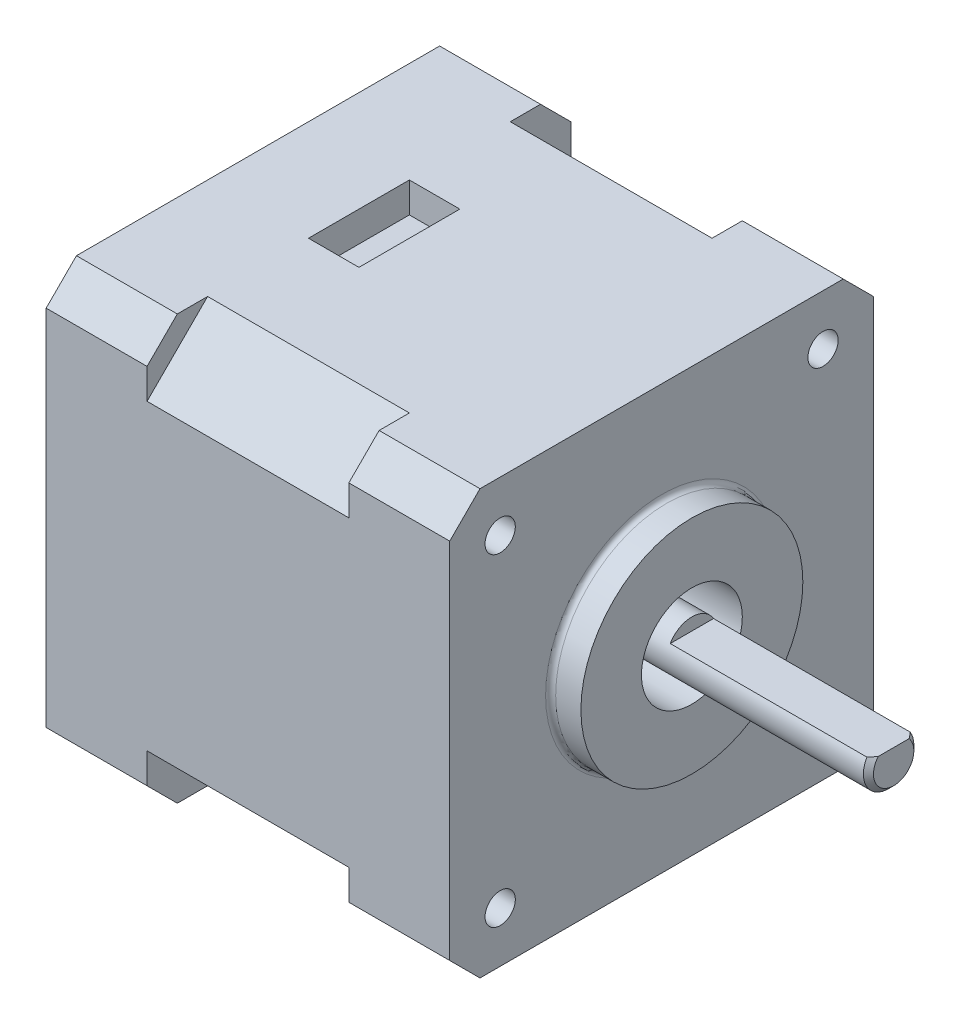
SolidWorks part; units mm, degrees
ref_plane "Plan de face" through (0, 0, 0) normal (0, 0, 1) x (1, 0, 0)
ref_plane "Plan de dessus" through (0, 0, 0) normal (0, 1, 0) x (1, 0, 0)
ref_plane "Plan de droite" through (0, 0, 0) normal (1, 0, 0) x (0, 0, -1)
sketch "Esquisse1" plane through (0, 0, 0) normal (1, 0, 0) x (0, 0, -1)
  line L0 (21, 0) -> (21, -36) construction
  line L1 (6, 0) -> (36, 0)
  line L2 (0, -6) -> (0, -36)
  line L3 (6, -42) -> (36, -42)
  line L4 (42, -6) -> (42, -36)
  line L5 (0, -21) -> (42, -21) construction
  line L6 (6, 0) -> (0, -6)
  line L7 (36, 0) -> (42, -6)
  line L8 (36, -42) -> (42, -36)
  line L9 (6, -42) -> (0, -36)
  dimension "D2" = 15
  dimension "D3" = 15
extrude "Boss.-Extru.1" add sketch "Esquisse1" along normal mid plane 20
sketch "Esquisse2" plane through (10, 0, 0) normal (1, 0, 0) x (0, 0, -1)
  line L0 (21, 0) -> (21, -42) construction
  line L1 (36, 0) -> (6, 0) construction
  line L2 (6, -42) -> (36, -42) construction
  line L3 (0, -21) -> (42, -21) construction
  line L4 (0, -6) -> (0, -36) construction
  line L5 (42, -36) -> (42, -6) construction
  line L7 (0, 0) -> (42, 0)
  line L8 (0, 0) -> (0, -42)
  line L9 (0, -42) -> (42, -42)
  line L10 (42, 0) -> (42, -42)
  line L11 (0, 0) -> (42, -42) construction
  line L12 (0, -42) -> (42, 0) construction
  point P12 (21, -21)
extrude "Boss.-Extru.2" add sketch "Esquisse2" along normal blind 10
sketch "Esquisse3" plane through (-10, 0, 0) normal (-1, 0, 0) x (0, 0, 1)
  line L0 (-21, 0) -> (-21, -42) construction
  line L1 (-36, 0) -> (-6, 0) construction
  line L2 (-6, -42) -> (-36, -42) construction
  line L3 (-42, -21) -> (0, -21) construction
  line L4 (-42, -36) -> (-42, -6) construction
  line L5 (0, -6) -> (0, -36) construction
  line L7 (-42, 0) -> (0, 0)
  line L8 (-42, 0) -> (-42, -42)
  line L9 (-42, -42) -> (0, -42)
  line L10 (0, 0) -> (0, -42)
  line L11 (-42, 0) -> (0, -42) construction
  line L12 (-42, -42) -> (0, 0) construction
  point P12 (-21, -21)
extrude "Boss.-Extru.3" add sketch "Esquisse3" along normal blind 10
sketch "Esquisse4" plane through (20, 0, 0) normal (1, 0, 0) x (0, 0, -1)
  line L0 (21, 0) -> (21, -42) construction
  line L1 (42, 0) -> (0, 0) construction
  line L2 (0, -42) -> (42, -42) construction
  line L3 (0, -21) -> (42, -21) construction
  line L4 (0, 0) -> (0, -42) construction
  line L5 (42, -42) -> (42, 0) construction
  circle A0 centre (21, -21) radius 11
  dimension "D1" = 22
extrude "Boss.-Extru.4" add sketch "Esquisse4" along normal blind 3
fillet "Congé1" radius 0.5 1 edges at (20, -21, -32)
sketch "Esquisse5" plane through (23, 0, 0) normal (1, 0, 0) x (0, 0, -1)
  circle A0 centre (21, -21) radius 5
  dimension "D1" = 10
extrude "Enlèv. mat.-Extru.1" cut sketch "Esquisse5" against normal blind 10
sketch "Esquisse6" plane through (13, 0, 0) normal (1, 0, 0) x (0, 0, -1)
  circle A0 centre (21, -21) radius 2.5
  dimension "D1" = 5
extrude "Boss.-Extru.5" add sketch "Esquisse6" along normal blind 30
sketch "Esquisse7" plane through (43, 0, 0) normal (1, 0, 0) x (0, 0, -1)
  line L0 (18.8536, -19.7181) -> (23.1464, -19.7181)
  arc A0 (23.1464, -19.7181) -> (18.8536, -19.7181) centre (21, -21) ccw
extrude "Enlèv. mat.-Extru.2" cut sketch "Esquisse7" against normal blind 20
chamfer "Chanfrein1" distance 0.5 angle 45 1 edges at (43, -23.5, -21)
sketch "Esquisse8" plane through (20, 0, 0) normal (1, 0, 0) x (0, 0, -1)
  line L0 (21, 0) -> (21, -42) construction
  line L1 (42, 0) -> (0, 0) construction
  line L2 (0, -42) -> (42, -42) construction
  line L3 (0, -21) -> (42, -21) construction
  line L4 (0, 0) -> (0, -42) construction
  line L5 (42, -42) -> (42, 0) construction
  circle A0 centre (5, -5) radius 1.5
  circle A1 centre (37, -5) radius 1.5
  circle A2 centre (5, -37) radius 1.5
  circle A3 centre (37, -37) radius 1.5
  dimension "D1" = 5
  dimension "D3" = 3
  dimension "D2" = 5
extrude "Enlèv. mat.-Extru.3" cut sketch "Esquisse8" against normal blind 5
sketch "Esquisse9" plane through (20, 0, 0) normal (1, 0, 0) x (0, 0, -1)
  line L0 (21, 0) -> (21, -42) construction
  line L1 (42, 0) -> (0, 0) construction
  line L2 (0, -42) -> (42, -42) construction
  line L3 (0, -21) -> (42, -21) construction
  line L4 (0, 0) -> (0, -42) construction
  line L5 (42, -42) -> (42, 0) construction
  line L6 (3, 0) -> (0, -3)
  line L7 (39, 0) -> (42, -3)
  line L8 (3, -42) -> (0, -39)
  line L9 (39, -42) -> (42, -39)
  line L10 (0, -3) -> (0, 0)
  line L11 (0, 0) -> (3, 0)
  line L12 (39, 0) -> (42, 0)
  line L13 (42, 0) -> (42, -3)
  line L14 (0, -39) -> (0, -42)
  line L15 (0, -42) -> (3, -42)
  line L16 (39, -42) -> (42, -42)
  line L17 (42, -42) -> (42, -39)
  dimension "D1" = 3
  dimension "D2" = 3
extrude "Enlèv. mat.-Extru.5" cut sketch "Esquisse9" against normal through all
sketch "Esquisse11" plane through (0, 0, 0) normal (0, 1, 0) x (1, 0, 0)
  line L0 (-20, 21) -> (20, 21) construction
  line L1 (-10, 26) -> (-5, 26)
  line L2 (-10, 26) -> (-10, 16)
  line L3 (-10, 16) -> (-5, 16)
  line L4 (-5, 26) -> (-5, 16)
  line L5 (-20, 3) -> (-20, 39) construction
  line L6 (20, 9.5) -> (20, 32.5) construction
  line L7 (-10, 36) -> (-10, 39) construction
  dimension "D1" = 5
  dimension "D2" = 10
extrude "Enlèv. mat.-Extru.6" cut sketch "Esquisse11" against normal blind 3
